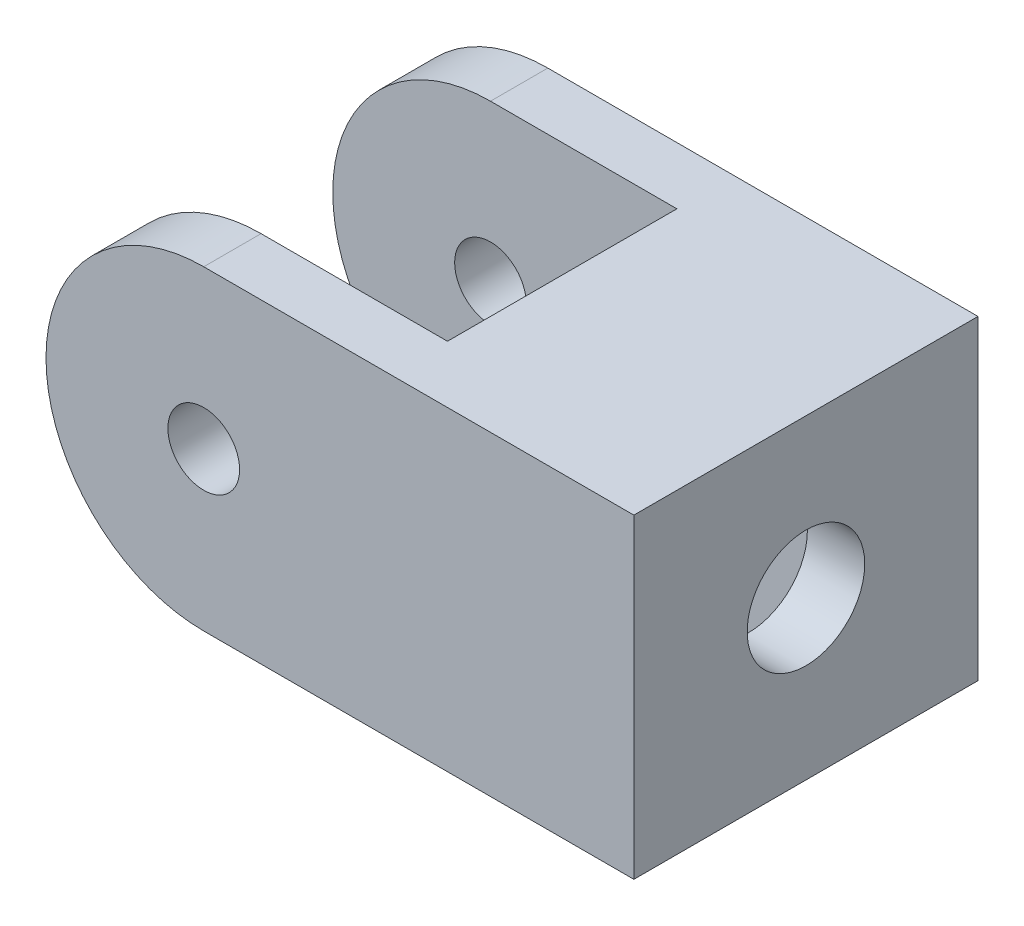
SolidWorks part; units mm, degrees
ref_plane "Front" through (0, 0, 0) normal (0, 0, 1) x (1, 0, 0)
ref_plane "Top" through (0, 0, 0) normal (0, 1, 0) x (1, 0, 0)
ref_plane "Right" through (0, 0, 0) normal (1, 0, 0) x (0, 0, -1)
sketch "Sketch1" plane through (0, 0, 0) normal (0, 0, 1) x (1, 0, 0)
  line L0 (0, 11) -> (30, 11)
  line L1 (30, 11) -> (30, -11)
  line L2 (30, -11) -> (0, -11)
  arc A0 (0, 11) -> (0, -11) centre (0, 0) ccw
  circle A1 centre (0, 0) radius 2.5
  dimension "D1" = 22
  dimension "D2" = 5
  dimension "D3" = 30
extrude "Boss-Extrude1" add sketch "Sketch1" along normal blind 24
sketch "Sketch2" plane through (0, 11, 0) normal (0, 1, 0) x (1, 0, 0)
  line L0 (-11, 0) -> (-11, -24) construction
  line L1 (-11, -4) -> (13, -4)
  line L2 (-11, -4) -> (-11, -20)
  line L3 (-11, -20) -> (13, -20)
  line L4 (13, -4) -> (13, -20)
  line L5 (-11, -4) -> (13, -20) construction
  line L6 (-11, -20) -> (13, -4) construction
  line L7 (-11, -12) -> (13, -12) construction
  point P4 (1, -12)
  dimension "D1" = 16
  dimension "D2" = 24
  dimension "D3" = 12
extrude "Cut-Extrude1" cut sketch "Sketch2" against normal through all
ref_plane "Plane1" through (26, 0, 0) normal (1, 0, 0) x (0, 0, -1)
sketch "Sketch4" plane through (26, 0, 0) normal (1, 0, 0) x (0, 0, -1)
  line L0 (-24, -11) -> (0, 11) construction
  line L1 (-24, 11) -> (0, -11) construction
  line L2 (-24, -11) -> (0, -11)
  line L3 (-5.5, 3.7528) -> (-12, 7.5056)
  line L4 (-12, 7.5056) -> (-18.5, 3.7528)
  line L5 (-18.5, 3.7528) -> (-18.5, -11)
  line L8 (-5.5, -11) -> (-5.5, 3.7528)
  line L10 (-8, -5.1962) -> (-6.751, -4.475) [skipped]
  line L11 (-16.499, -4.908) -> (-15.25, -5.6292) [skipped]
  circle A0 centre (-12, 0) radius 6.5 construction
  dimension "D1" = 13
extrude "Cut-Extrude2" cut sketch "Sketch4" against normal blind 6.8 contours L2 L8 L3 L4 L5
sketch "Sketch6" plane through (30, 0, 0) normal (1, 0, 0) x (0, 0, -1)
  line L0 (-24, -11) -> (0, 11) construction
  circle A0 centre (-12, 0) radius 4.1
  dimension "D1" = 8.2
extrude "Cut-Extrude3" cut sketch "Sketch6" against normal up to surface (17 mm away) up to face at (13, 0, 12)
